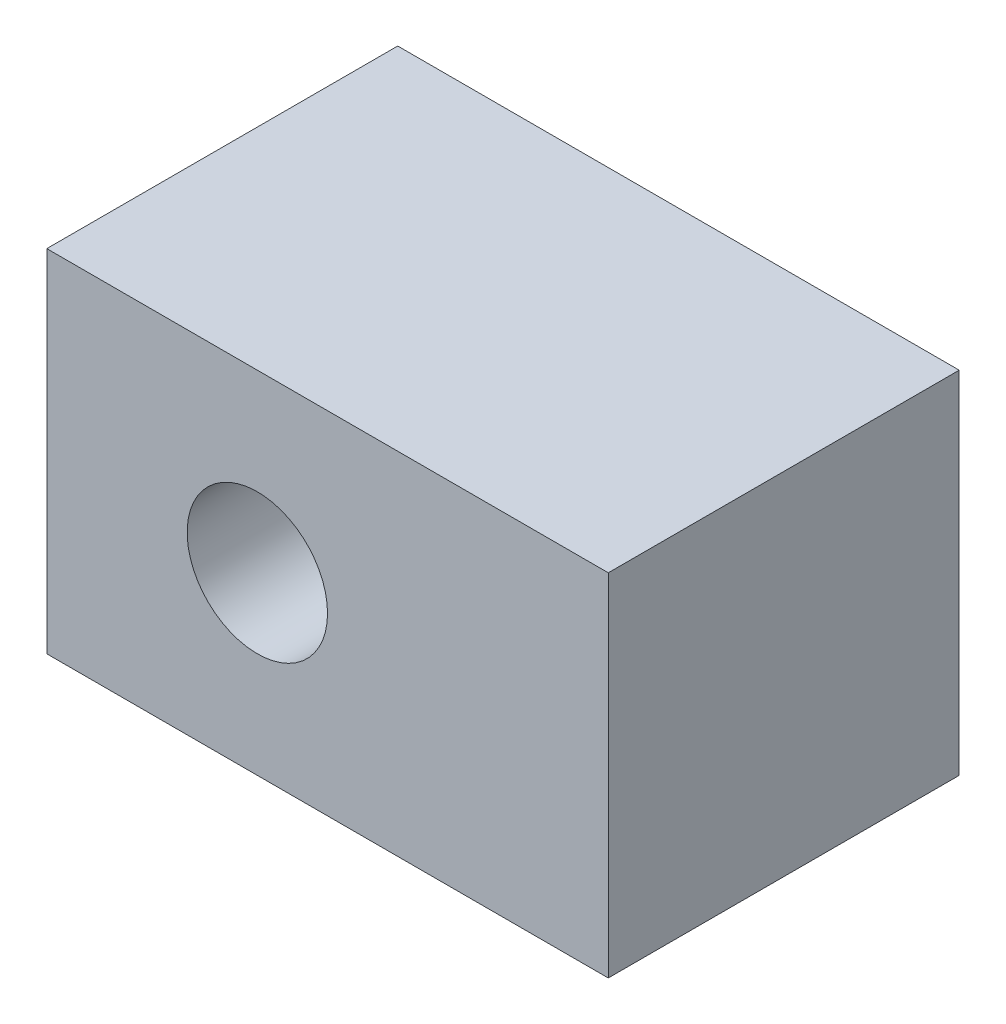
SolidWorks part; units mm, degrees
ref_plane "Спереди" through (0, 0, 0) normal (0, 0, 1) x (1, 0, 0)
ref_plane "Сверху" through (0, 0, 0) normal (0, 1, 0) x (1, 0, 0)
ref_plane "Справа" through (0, 0, 0) normal (1, 0, 0) x (0, 0, -1)
sketch "Эскиз1" plane through (0, 0, 0) normal (0, 0, 1) x (1, 0, 0)
  line L0 (-30, 0) -> (0, 0) construction
  line L1 (-30, 25) -> (50, 25)
  line L2 (-30, 25) -> (-30, -25)
  line L3 (-30, -25) -> (50, -25)
  line L4 (50, 25) -> (50, -25)
  circle A0 centre (0, 0) radius 10
  dimension "D1" = 20
  dimension "D2" = 80
  dimension "D3" = 50
  dimension "D4" = 30
extrude "Бобышка-Вытянуть1" add sketch "Эскиз1" along normal mid plane 50
